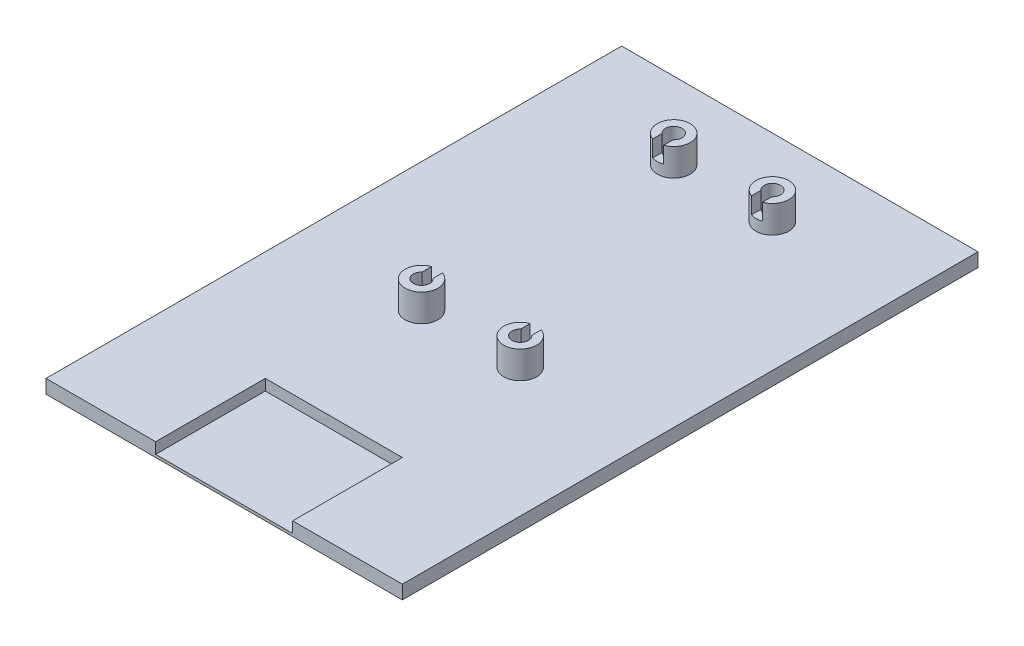
SolidWorks part; units mm, degrees
ref_plane "Front Plane" through (0, 0, 0) normal (0, 0, 1) x (1, 0, 0)
ref_plane "Top Plane" through (0, 0, 0) normal (0, 1, 0) x (1, 0, 0)
ref_plane "Right Plane" through (0, 0, 0) normal (1, 0, 0) x (0, 0, -1)
sketch "Sketch1" plane through (0, 0, 0) normal (0, 1, 0) x (1, 0, 0)
  line L1 (-30.5, 50.5) -> (30.5, 50.5)
  line L2 (-30.5, 50.5) -> (-30.5, -50.5)
  line L3 (-30.5, -50.5) -> (30.5, -50.5)
  line L4 (30.5, 50.5) -> (30.5, -50.5)
  dimension "D1" = 101
  dimension "D2" = 61
  dimension "D3" = 30.5
  dimension "D4" = 50.5
extrude "Boss-Extrude1" add sketch "Sketch1" along normal blind 2
sketch "Sketch2" plane through (0, 2, 0) normal (0, 1, 0) x (1, 0, 0)
  line L0 (30.5, -50.5) -> (30.5, 50.5) construction
  line L1 (32.5, -52.5) -> (-32.5, -52.5)
  line L2 (32.5, -52.5) -> (32.5, 52.5)
  line L3 (32.5, 52.5) -> (-32.5, 52.5)
  line L4 (-32.5, -52.5) -> (-32.5, 52.5)
  line L6 (30.5, 50.5) -> (-30.5, 50.5) construction
  dimension "D1" = 105
  dimension "D2" = 65
  dimension "D3" = 2
  dimension "D4" = 2
extrude "Boss-Extrude2" add sketch "Sketch2" along normal blind 2.5
sketch "Sketch4" plane through (0, 4.5, 0) normal (0, 1, 0) x (1, 0, 0)
  line L0 (32.5, -52.5) -> (32.5, 52.5) construction
  line L5 (32.5, 52.5) -> (-32.5, 52.5) construction
  line L6 (-32.5, 52.5) -> (-32.5, -52.5) construction
  line L7 (-32.5, -52.5) -> (32.5, -52.5) construction
  circle A0 centre (9, -7.5) radius 1.5
  circle A1 centre (-9, -7.5) radius 1.5
  circle A2 centre (9, 38.5) radius 1.5
  circle A3 centre (-9, 38.5) radius 1.5
  circle A4 centre (-9, -7.5) radius 3
  circle A5 centre (9, -7.5) radius 3
  circle A6 centre (9, 38.5) radius 3
  circle A7 centre (-9, 38.5) radius 3
  dimension "D5" = 3
  dimension "D6" = 3
  dimension "D7" = 3
  dimension "D8" = 3
  dimension "D17" = 6
  dimension "D18" = 6
  dimension "D19" = 6
  dimension "D20" = 6
  dimension "D21" = 23.5
  dimension "D22" = 45
  dimension "D23" = 23.5
  dimension "D24" = 45
  dimension "D25" = 23.5
  dimension "D26" = 14
  dimension "D27" = 14
  dimension "D28" = 23.5
extrude "Boss-Extrude3" add sketch "Sketch4" along normal blind 5
sketch "Sketch5" plane through (0, 4.5, 0) normal (0, 1, 0) x (1, 0, 0)
  line L0 (32.5, -52.5) -> (32.5, 52.5) construction
  line L1 (12.5, -64.5) -> (-12.5, -64.5)
  line L2 (12.5, -64.5) -> (12.5, -32.5)
  line L3 (12.5, -32.5) -> (-12.5, -32.5)
  line L4 (-12.5, -64.5) -> (-12.5, -32.5)
  line L5 (-32.5, -52.5) -> (32.5, -52.5) construction
  dimension "D1" = 20
  dimension "D2" = 32
  dimension "D3" = 25
  dimension "D4" = 20
extrude "Cut-Extrude1" cut sketch "Sketch5" against normal blind 2
sketch "Sketch6" plane through (0, 9.5, 0) normal (0, 1, 0) x (1, 0, 0)
  line L1 (10, -8) -> (8, -8)
  line L2 (10, -8) -> (10, -4)
  line L3 (10, -4) -> (8, -4)
  line L4 (8, -8) -> (8, -4)
  line L5 (-8, -8) -> (-10, -8)
  line L6 (-8, -8) -> (-8, -4)
  line L7 (-8, -4) -> (-10, -4)
  line L8 (-10, -8) -> (-10, -4)
  line L9 (10, 39) -> (8, 39)
  line L10 (10, 39) -> (10, 35)
  line L11 (10, 35) -> (8, 35)
  line L12 (8, 39) -> (8, 35)
  line L13 (-8, 39) -> (-10, 39)
  line L14 (-8, 39) -> (-8, 35)
  line L15 (-8, 35) -> (-10, 35)
  line L16 (-10, 39) -> (-10, 35)
  circle A0 centre (9, -7.5) radius 1.5 construction
  circle A1 centre (9, -7.5) radius 1.5 construction
  circle A2 centre (-9, -7.5) radius 1.5 construction
  circle A3 centre (9, 38.5) radius 1.5 construction
  circle A4 centre (9, 38.5) radius 1.5 construction
  circle A5 centre (-9, 38.5) radius 1.5 construction
  dimension "D1" = 2
  dimension "D2" = 3.5
  dimension "D3" = 1
  dimension "D4" = 4
  dimension "D5" = 4
  dimension "D6" = 2
  dimension "D7" = 1
  dimension "D8" = 0.5
  dimension "D9" = 4
  dimension "D10" = 4
  dimension "D11" = 2
  dimension "D12" = 2
  dimension "D13" = 1
  dimension "D14" = 0.5
  dimension "D15" = 1
  dimension "D16" = 0.5
extrude "Cut-Extrude2" cut sketch "Sketch6" against normal blind 3
sketch "Sketch7" plane through (0, 0, 0) normal (0, -1, 0) x (1, 0, 0)
  line L0 (-30.5, -50.5) -> (-30.5, 50.5) construction
  line L1 (-16.5, 28.5) -> (16.5, 28.5)
  line L2 (-26.5, 28.5) -> (-26.5, -46.5)
  line L3 (-26.5, -46.5) -> (26.5, -46.5)
  line L4 (26.5, 28.5) -> (26.5, -46.5)
  line L5 (30.5, -50.5) -> (-30.5, -50.5) construction
  line L6 (30.5, 50.5) -> (30.5, -50.5) construction
  line L7 (-30.5, 50.5) -> (30.5, 50.5) construction
  line L10 (-26.5, 28.5) -> (-26.5, 46.5)
  line L11 (-26.5, 46.5) -> (-16.5, 46.5)
  line L12 (-16.5, 28.5) -> (-16.5, 46.5)
  line L14 (26.5, 28.5) -> (26.5, 46.5)
  line L15 (26.5, 46.5) -> (16.5, 46.5)
  line L16 (16.5, 28.5) -> (16.5, 46.5)
  line L17 (-30.5, 50.5) -> (30.5, 50.5) construction
  line L18 (-30.5, -50.5) -> (-30.5, 50.5) construction
  dimension "D1" = 4
  dimension "D2" = 4
  dimension "D3" = 4
  dimension "D4" = 22
  dimension "D5" = 4
  dimension "D6" = 4
  dimension "D7" = 14
  dimension "D8" = 14
extrude "Cut-Extrude3" cut sketch "Sketch7" against normal blind 2.5
